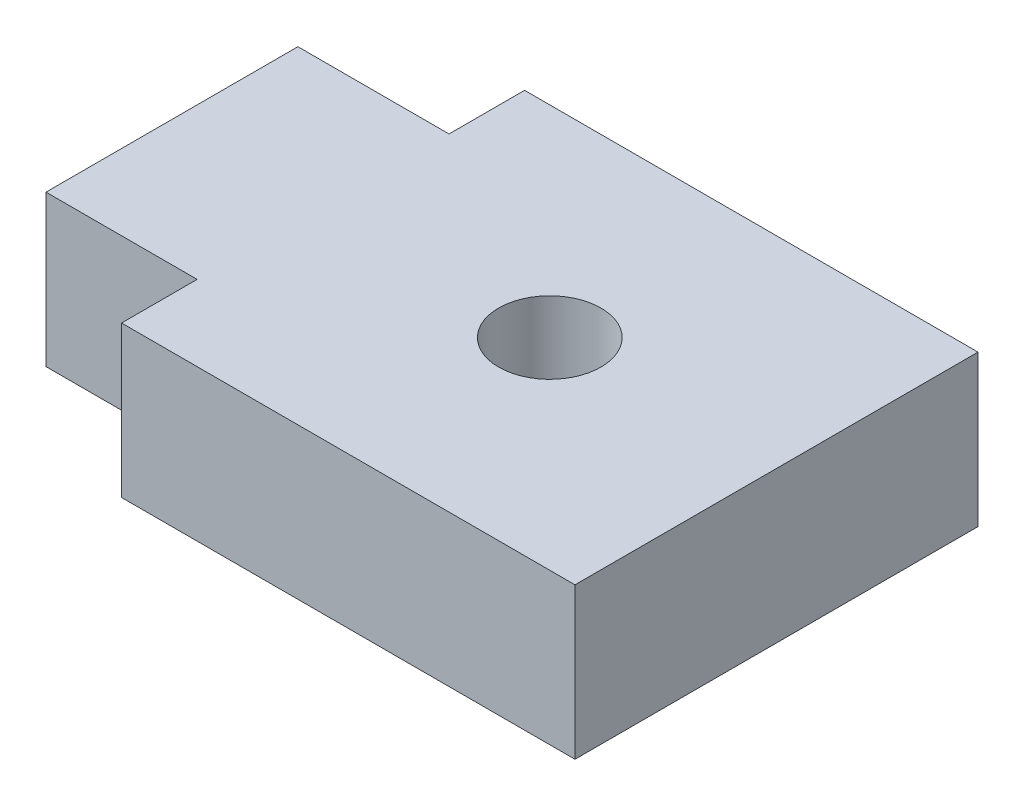
SolidWorks part; units mm, degrees
material "PC High Viscosity"
ref_plane "Front Plane" through (0, 0, 0) normal (0, 0, 1) x (1, 0, 0)
ref_plane "Top Plane" through (0, 0, 0) normal (0, 1, 0) x (1, 0, 0)
ref_plane "Right Plane" through (0, 0, 0) normal (1, 0, 0) x (0, 0, -1)
sketch "Sketch1" plane through (0, 0, 0) normal (0, 1, 0) x (1, 0, 0)
  line L0 (0, -4) -> (0, 4) construction
  line L1 (-4.5, -4) -> (4.5, -4)
  line L2 (-4.5, -4) -> (-4.5, 4)
  line L3 (-4.5, 4) -> (4.5, 4)
  line L4 (4.5, -4) -> (4.5, 4)
  line L5 (-4.5, -4) -> (4.5, 4) construction
  line L6 (-4.5, 4) -> (4.5, -4) construction
  point P0 (0, 0)
  dimension "D1" = 9
  dimension "D2" = 8
extrude "Boss-Extrude1" add sketch "Sketch1" along normal blind 3
sketch "Sketch2" plane through (0, 3, 0) normal (0, 1, 0) x (1, 0, 0)
  line L1 (-7.5, -2.5) -> (-4.5, -2.5)
  line L2 (-7.5, -2.5) -> (-7.5, 2.5)
  line L3 (-7.5, 2.5) -> (-4.5, 2.5)
  line L4 (-4.5, -2.5) -> (-4.5, 2.5)
  line L5 (-7.5, -2.5) -> (-4.5, 2.5) construction
  line L6 (-7.5, 2.5) -> (-4.5, -2.5) construction
  line L11 (-4.5, -4) -> (-4.5, 4) construction
  point P0 (-6, 0)
  point P7 (0, 0)
  dimension "D2" = 5
  dimension "D1" = 3
extrude "Boss-Extrude2" add sketch "Sketch2" against normal up to surface (3 mm away) up to face at (0, 0, 0)
sketch "Sketch3" plane through (0, 3, 0) normal (0, 1, 0) x (1, 0, 0)
  circle A0 centre (0, 0) radius 1.016
  dimension "D1" = 2.032
extrude "Cut-Extrude1" cut sketch "Sketch3" against normal through all
equation "\"pulley_pitch_diam\"= 12.73mm"
equation "\"pulley_total_width\"= 16mm"
equation "\"pulley_total_diam\"= 16mm"
equation "\"belt_width\"= 6mm"
equation "\"material_thickness\"= 3mm"
equation "\"shaft_diam\"= 8mm"
equation "\"bearing_od\"= 22mm"
equation "\"bearing_thickness\"= 7mm"
equation "\"D1@Sketch1\"=\"material_thickness\" * 3"
equation "\"D1@Boss-Extrude1\"=\"material_thickness\""
equation "\"D1@Sketch2\"=\"material_thickness\""
